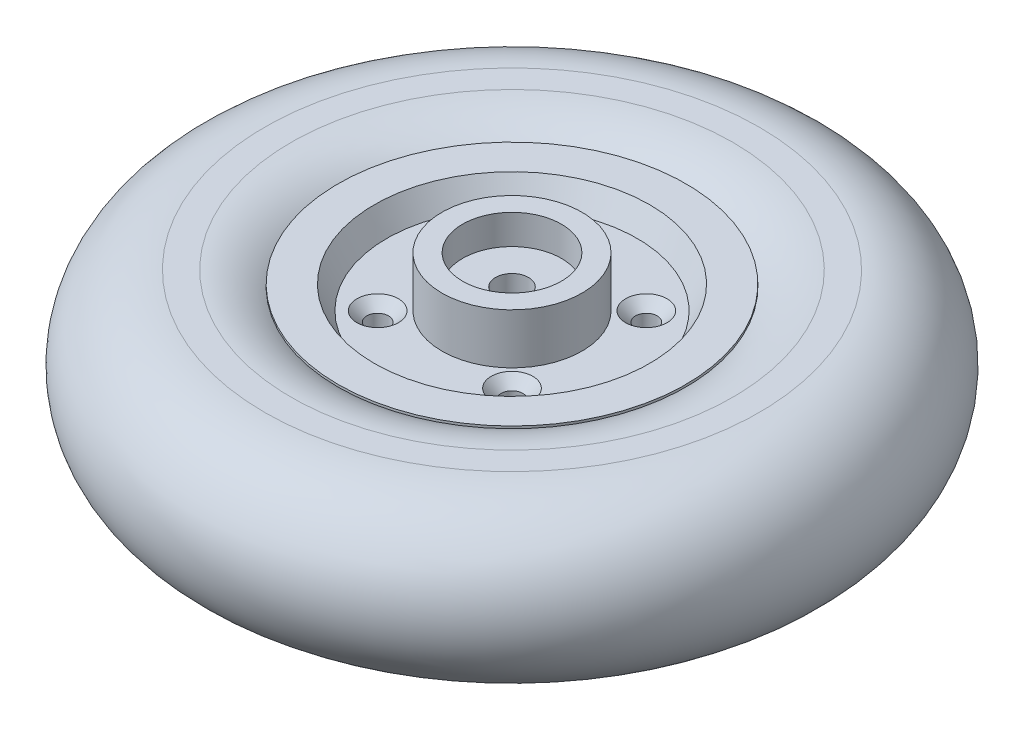
SolidWorks part; units mm, degrees
ref_plane "前基準面" through (0, 0, 0) normal (0, 0, 1) x (1, 0, 0)
ref_plane "上基準面" through (0, 0, 0) normal (0, 1, 0) x (1, 0, 0)
ref_plane "右基準面" through (0, 0, 0) normal (1, 0, 0) x (0, 0, -1)
sketch "草圖1" plane through (0, 0, 0) normal (0, 0, 1) x (1, 0, 0)
  line L0 (0, 152.2311) -> (0, -121.6179) construction
  line L1 (0, 0) -> (36.2427, 0) construction
  line L2 (15, 29.5) -> (21.25, 29.5)
  line L3 (5, 20.5) -> (5, -20.5)
  line L4 (15, -29.5) -> (21.25, -29.5)
  line L5 (21.25, 29.5) -> (21.25, 14.25)
  line L6 (41.75, 21.25) -> (52.75, 21.25)
  line L7 (5, -20.5) -> (15, -20.5)
  line L8 (41.75, -21.25) -> (52.75, -21.25)
  line L9 (52.75, 21.25) -> (52.75, -21.25)
  line L10 (21.25, -14.25) -> (21.25, -29.5)
  line L11 (5, 20.5) -> (15, 20.5)
  line L12 (15, -20.5) -> (15, -29.5)
  line L13 (41.75, 21.25) -> (38, 14.25)
  line L14 (15, 20.5) -> (15, 29.5)
  line L15 (38, 14.25) -> (21.25, 14.25)
  line L16 (41.75, -21.25) -> (38, -14.25)
  line L17 (38, -14.25) -> (21.25, -14.25)
  dimension "D1" = 59
  dimension "D2" = 42.5
  dimension "D3" = 42.5
  dimension "D4" = 105.5
  dimension "D5" = 30
  dimension "D6" = 10
  dimension "D7" = 9
  dimension "D8" = 7
  dimension "D9" = 11
  dimension "D10" = 76
revolve "旋轉1" add sketch "草圖1" angle 360 about L0
sketch "草圖2" plane through (0, 0, 0) normal (0, 0, 1) x (1, 0, 0)
  line L0 (-75, 0) -> (-67, 0) construction
  line L1 (-75, 25) -> (-67, 25)
  line L2 (-75, -25) -> (-67, -25)
  line L3 (0, 0) -> (0, 44.6033) construction
  arc A0 (-75, 25) -> (-75, -25) centre (-75, 0) ccw
  arc A1 (-67, -25) -> (-67, 25) centre (-67, 0) ccw
  point P3 (-71, 0)
  point P17 (-100, 0)
  dimension "D1" = 50
  dimension "D2" = 200
  dimension "D3" = 8
revolve "旋轉2" add sketch "草圖2" angle 360 about L3
hole_wizard "M6 平錐坑頭螺釘的錐孔1" positions "草圖4" profile "草圖3" countersink size "M6" standard "JIS" end condition through all
sketch "草圖4" plane through (0, 14.25, 0) normal (0, 1, 0) x (1, 0, 0)
  line L0 (0, 30.3007) -> (0, 0) construction
  line L1 (0, 0) -> (-30.2832, 0) construction
  point P0 (-20.375, -20.375)
  point P6 (-20.375, 20.375)
  point P7 (20.375, -20.375)
  point P8 (20.375, 20.375)
  dimension "D1" = 40.75
  dimension "D2" = 40.75
sketch "草圖3" plane through (-20.375, 14.25, 20.375) normal (1, 0, 0) x (0, 0, 1)
  line L0 (0, 0) -> (0, 43.75)
  line L1 (0, 43.75) -> (3.3, 43.75)
  line L2 (3.3, 43.75) -> (3.3, 3)
  line L3 (3.3, 3) -> (6.3, 0)
  line L5 (6.3, 0) -> (0, 0)
  line L6 (-3.3, 3) -> (-6.3, 0) construction
  line L11 (0, -6.35) -> (0, 107.95) construction
  dimension "貫穿孔直徑" = 6.6
  dimension "貫穿孔深度" = 43.75
  dimension "近端錐孔直徑" = 12.6
  dimension "近端錐孔角度" = 90
